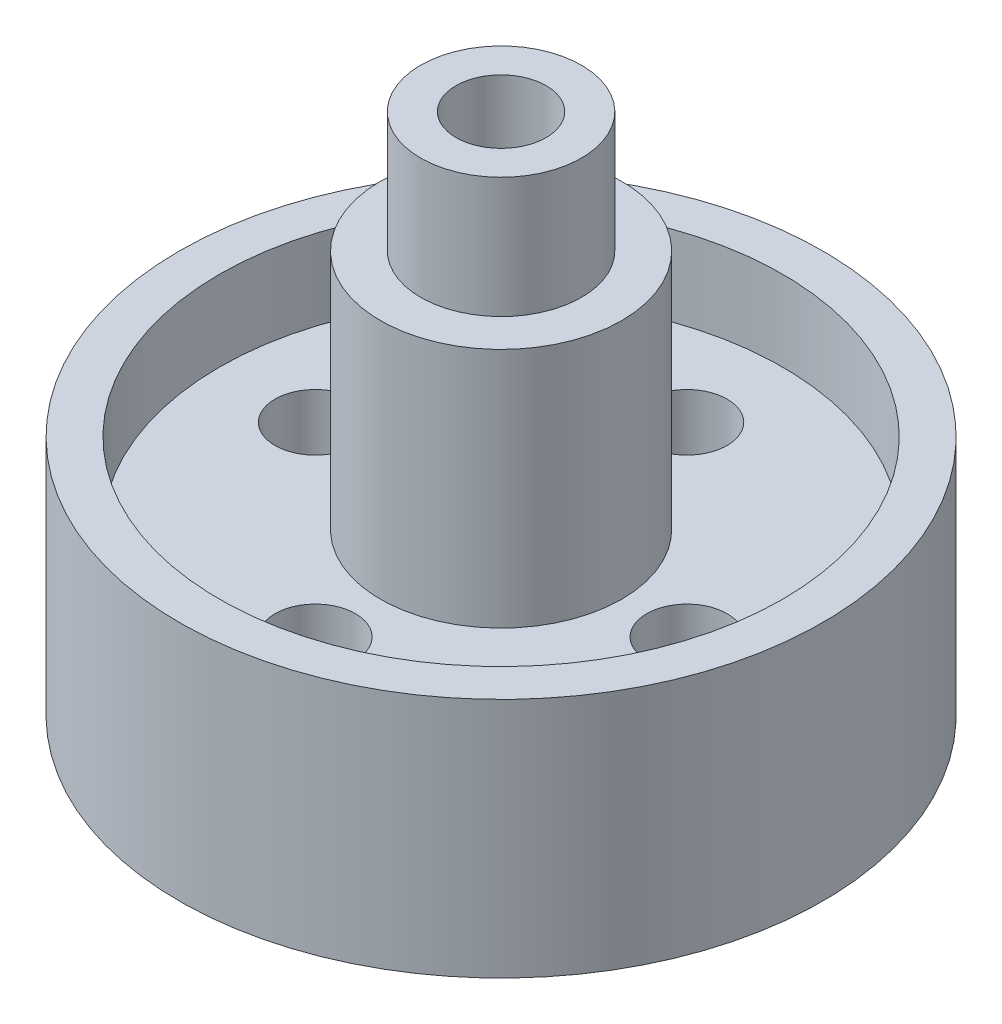
SolidWorks part; units mm, degrees
ref_plane "Front Plane" through (0, 0, 0) normal (0, 0, 1) x (1, 0, 0)
ref_plane "Top Plane" through (0, 0, 0) normal (0, 1, 0) x (1, 0, 0)
ref_plane "Right Plane" through (0, 0, 0) normal (1, 0, 0) x (0, 0, -1)
sketch "Sketch1" plane through (0, 0, 0) normal (0, 0, 1) x (1, 0, 0)
  line L0 (0, 0) -> (50.8, 0)
  line L1 (50.8, 0) -> (50.8, 25.4)
  line L2 (50.8, 25.4) -> (0, 25.4)
  line L3 (0, 25.4) -> (0, 0)
  dimension "D1" = 50.8
  dimension "D2" = 25.4
revolve "Revolve1" add sketch "Sketch1" angle 360 about L3
sketch "Sketch2" plane through (0, 25.4, 0) normal (0, 1, 0) x (1, 0, 0)
  circle A0 centre (0, 0) radius 29.337 construction
  circle A1 centre (29.337, 0) radius 6.35
  circle A2 centre (0, -29.337) radius 6.35
  circle A3 centre (-29.337, 0) radius 6.35
  circle A4 centre (0, 29.337) radius 6.35
  point P14 (0, 0)
  dimension "D1" = 58.674
  dimension "D2" = 12.7
  dimension "D3" = 4
extrude "Cut-Extrude1" cut sketch "Sketch2" against normal through all
sketch "Sketch4" plane through (0, 25.4, 0) normal (0, 1, 0) x (1, 0, 0)
  circle A1 centre (0, 0) radius 50.8
  circle A2 centre (0, 0) radius 44.45
  circle A3 centre (0, 0) radius 44.45
  dimension "D1" = 6.35
extrude "Boss-Extrude1" add sketch "Sketch4" along normal blind 12.7
sketch "Sketch6" plane through (0, 25.4, 0) normal (0, 1, 0) x (1, 0, 0)
  circle A0 centre (0, 0) radius 19.05
  dimension "D1" = 38.1
extrude "Boss-Extrude2" add sketch "Sketch6" along normal blind 38.1
sketch "Sketch7" plane through (0, 63.5, 0) normal (0, 1, 0) x (1, 0, 0)
  circle A0 centre (0, 0) radius 12.7
  dimension "D1" = 25.4
extrude "Boss-Extrude3" add sketch "Sketch7" along normal blind 19.05
sketch "Sketch8" plane through (0, 82.55, 0) normal (0, 1, 0) x (1, 0, 0)
  circle A0 centre (0, 0) radius 7.112
  dimension "D1" = 14.224
extrude "Cut-Extrude2" cut sketch "Sketch8" against normal through all
